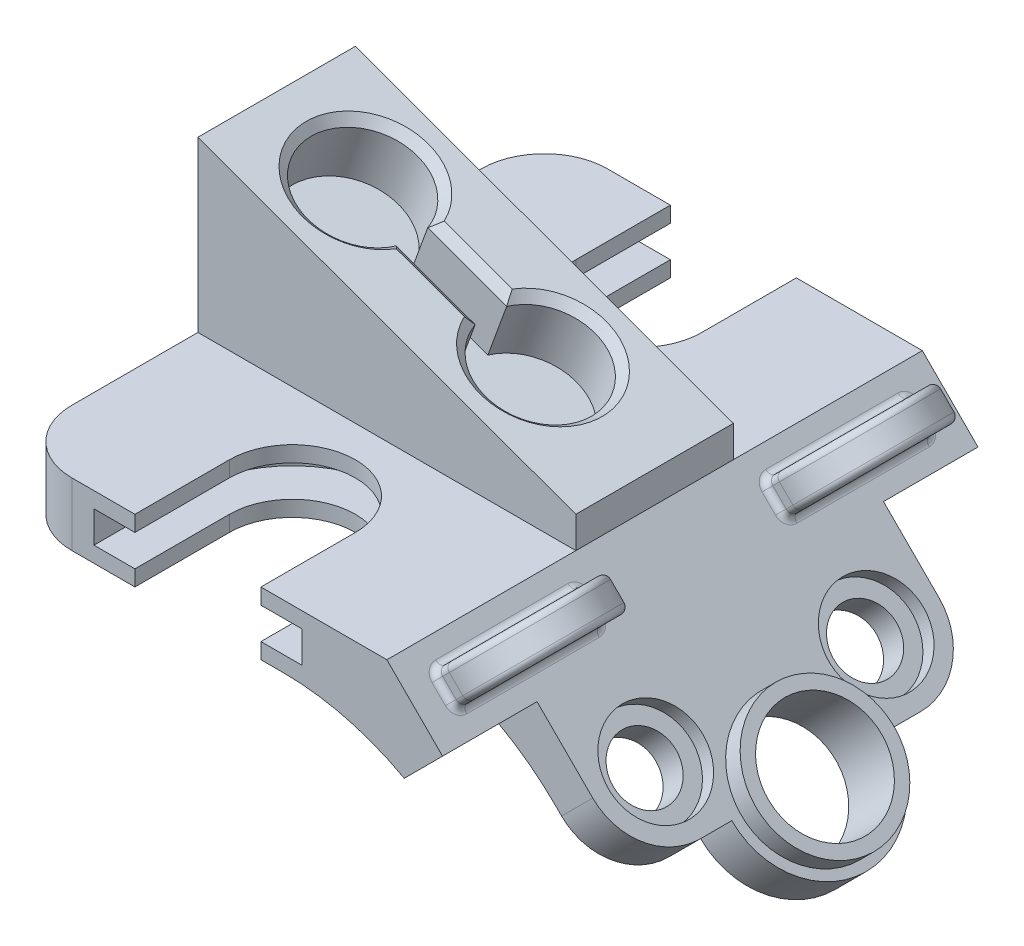
SolidWorks part; units mm, degrees
material "Alloy Steel (SS)"
ref_plane "Front Plane" through (0, 0, 0) normal (0, 0, 1) x (1, 0, 0)
ref_plane "Top Plane" through (0, 0, 0) normal (0, 1, 0) x (1, 0, 0)
ref_plane "Right Plane" through (0, 0, 0) normal (1, 0, 0) x (0, 0, -1)
sketch "Sketch1" plane through (0, 0, 0) normal (0, 0, 1) x (1, 0, 0)
  line L0 (0, 0) -> (0, 12.7)
  line L1 (0, 12.7) -> (76.2, 12.7)
  line L2 (76.2, 12.7) -> (118.8562, -29.9562)
  line L3 (118.8562, -29.9562) -> (112.57, -36.2424)
  line L4 (112.57, -36.2424) -> (91.2066, -14.879)
  line L5 (55.2856, 0) -> (0, 0)
  arc A0 (91.2066, -14.879) -> (55.2856, 0) centre (55.2856, -50.8) ccw
  dimension "D6" = 50.8
  dimension "D1" = 8.89
  dimension "D2" = 135
  dimension "D3" = 12.7
  dimension "D4" = 76.2
  dimension "D5" = 60.325
extrude "Boss-Extrude1" add sketch "Sketch1" along normal mid plane 107.95
sketch "Sketch2" plane through (0, 12.7, 0) normal (0, 1, 0) x (1, 0, 0)
  line L0 (25.4, 53.975) -> (25.4, 34.925)
  line L1 (76.2, 53.975) -> (0, 53.975) construction
  line L2 (50.8, 53.975) -> (50.8, 34.925)
  line L3 (25.4, 53.975) -> (50.8, 53.975)
  line L4 (0, -53.975) -> (0, 53.975) construction
  line L5 (0, 0) -> (76.2, 0) construction
  line L6 (76.2, -53.975) -> (76.2, 53.975) construction
  line L7 (25.4, -53.975) -> (50.8, -53.975)
  line L8 (50.8, -53.975) -> (50.8, -34.925)
  line L9 (25.4, -53.975) -> (25.4, -34.925)
  arc A0 (25.4, 34.925) -> (50.8, 34.925) centre (38.1, 34.925) ccw
  arc A1 (25.4, -34.925) -> (50.8, -34.925) centre (38.1, -34.925) cw
  point P8 (38.1, 53.975)
  dimension "D1" = 19.05
  dimension "D2" = 12.7
  dimension "D3" = 25.4
extrude "Cut-Extrude1" cut sketch "Sketch2" against normal through all
ref_plane "Plane1" through (0, 6.35, 0) normal (0, 1, 0) x (1, 0, 0)
sketch "Sketch4" plane through (0, 6.35, 0) normal (0, 1, 0) x (1, 0, 0)
  line L0 (59.055, -34.925) -> (59.055, -53.975)
  line L1 (76.2, -53.975) -> (50.8, -53.975) construction
  line L2 (59.055, -53.975) -> (17.145, -53.975)
  line L3 (17.145, -53.975) -> (17.145, -34.925)
  line L4 (25.4, -53.975) -> (0, -53.975) construction
  line L5 (0, 0) -> (76.2, 0) construction
  line L6 (50.8, -53.975) -> (50.8, -34.925) construction
  line L7 (76.2, -53.975) -> (76.2, 53.975) construction
  line L8 (25.4, -34.925) -> (25.4, -53.975) construction
  line L9 (17.145, 53.975) -> (17.145, 34.925)
  line L10 (59.055, 53.975) -> (17.145, 53.975)
  line L11 (59.055, 34.925) -> (59.055, 53.975)
  arc A0 (59.055, -34.925) -> (17.145, -34.925) centre (38.1, -34.925) ccw
  arc A1 (59.055, 34.925) -> (17.145, 34.925) centre (38.1, 34.925) cw
  dimension "D1" = 8.255
extrude "Cut-Extrude2" cut sketch "Sketch4" against normal mid plane 6.35
sketch "Sketch5" plane through (0, 0, 0) normal (0, 0, 1) x (1, 0, 0)
  line L0 (0, 12.7) -> (0, 46.7845)
  line L1 (0, 46.7845) -> (76.2, 19.05)
  line L2 (76.2, 19.05) -> (76.2, 12.7)
  line L3 (76.2, 12.7) -> (0, 12.7)
  dimension "D1" = 6.35
  dimension "D2" = 20
extrude "Boss-Extrude2" add sketch "Sketch5" along normal mid plane 31.75
sketch "Sketch6" plane through (15.0363, 41.3118, 0) normal (0.342, 0.9397, 0) x (0.9397, -0.342, 0)
  line L0 (-16.0013, -15.875) -> (-16.0013, 15.875) construction
  line L1 (13.6317, 3.175) -> (30.5658, 3.175)
  line L2 (13.6317, -3.175) -> (30.5658, -3.175)
  line L3 (3.0487, 0) -> (41.1487, 0) construction
  arc A0 (13.6317, 3.175) -> (13.6317, -3.175) centre (3.0487, 0) ccw
  arc A1 (30.5658, -3.175) -> (30.5658, 3.175) centre (41.1487, 0) ccw
  dimension "D1" = 22.098
  dimension "D2" = 19.05
  dimension "D3" = 38.1
  dimension "D4" = 6.35
  dimension "D5" = 3.175
extrude "Cut-Extrude3" cut sketch "Sketch6" against normal blind 12.7
chamfer "Chamfer1" distance 1.651 angle 45 4 edges at (64.0861, 23.4591, 0) (35.8023, 33.7536, 3.175) (7.5185, 44.048, 0) (35.8023, 33.7536, -3.175)
sketch "Sketch7" plane through (44.45, 44.45, 0) normal (0.7071, 0.7071, 0) x (0, 0, -1)
  line L0 (-53.975, -44.9013) -> (-53.975, -60.7763) construction
  line L1 (-53.975, -105.2263) -> (-53.975, -44.9013) construction
  line L2 (-53.975, -60.7763) -> (-34.925, -60.7763)
  line L3 (-34.925, -60.7763) -> (-34.925, -89.3513)
  line L4 (-34.925, -89.3513) -> (-15.875, -89.3513)
  line L8 (15.875, -89.3513) -> (34.925, -89.3513)
  line L9 (34.925, -89.3513) -> (34.925, -60.7763)
  line L10 (34.925, -60.7763) -> (53.975, -60.7763)
  line L11 (53.975, -105.2263) -> (53.975, -44.9013) construction
  line L12 (53.975, -60.7763) -> (53.975, -44.9013) construction
  line L13 (53.975, -44.9013) -> (-53.975, -44.9013) construction
  line L14 (-53.975, -60.7763) -> (-53.975, -105.2263)
  line L15 (-53.975, -105.2263) -> (53.975, -105.2263) construction
  line L17 (53.975, -105.2263) -> (53.975, -60.7763)
  arc A0 (-15.875, -89.3513) -> (15.875, -89.3513) centre (0, -89.3513) ccw
  line M16 (53.975, -105.2263) -> (53.975, -44.9013)
  line M20 (-53.975, -44.9013) -> (-53.975, -105.2263)
  line M21 (-53.975, -105.2263) -> (53.975, -105.2263)
  dimension "D5" = 15.875
  dimension "D1" = 15.875
  dimension "D2" = 19.05
  dimension "D3" = 28.575
  dimension "D4" = 19.05
  dimension "D6" = 53.975
extrude "Cut-Extrude4" cut sketch "Sketch7" against normal blind 12.7 contours A0 L4 L3 L2 M20 M21 | A0 L10 L9 L8 M21 M16
fillet "Fillet1" radius 12.7 4 edges at (0, 6.35, 53.975) (0, 6.35, -53.975) (104.4878, -21.874, -34.925) (104.4878, -21.874, 34.925)
sketch "Sketch9" plane through (44.45, 44.45, 0) normal (0.7071, 0.7071, 0) x (0, 0, -1)
  circle A0 centre (-22.225, -76.6513) radius 6.35
  circle A1 centre (22.225, -76.6513) radius 6.35
  dimension "D1" = 12.7
extrude "Cut-Extrude5" cut sketch "Sketch9" against normal blind 12.7
sketch "Sketch10" plane through (44.45, 44.45, 0) normal (0.7071, 0.7071, 0) x (0, 0, -1)
  circle A0 centre (-22.225, -76.6513) radius 9.525
  circle A1 centre (22.225, -76.6513) radius 9.525
  dimension "D1" = 19.05
extrude "Cut-Extrude6" cut sketch "Sketch10" against normal blind 3.175
sketch "Sketch11" plane through (44.45, 44.45, 0) normal (0.7071, 0.7071, 0) x (0, 0, -1)
  circle A0 centre (0, -89.3513) radius 13.97
  dimension "D1" = 27.94
extrude "Boss-Extrude3" add sketch "Sketch11" along normal mid plane 8.255
sketch "Sketch12" plane through (47.3686, 47.3686, 0) normal (0.7071, 0.7071, 0) x (0, 0, -1)
  circle A0 centre (0, -89.3513) radius 11.43
  dimension "D1" = 22.86
extrude "Cut-Extrude7" cut sketch "Sketch12" against normal through all
sketch "Sketch13" plane through (44.45, 44.45, 0) normal (0.7071, 0.7071, 0) x (0, 0, -1)
  line L0 (-53.975, -60.7763) -> (-53.975, -44.9013) construction
  line L1 (-47.879, -49.6638) -> (-18.669, -49.6638)
  line L2 (-47.879, -49.6638) -> (-47.879, -56.0138)
  line L3 (-47.879, -56.0138) -> (-18.669, -56.0138)
  line L4 (-18.669, -49.6638) -> (-18.669, -56.0138)
  line L5 (-47.879, -49.6638) -> (-18.669, -56.0138) construction
  line L6 (-47.879, -56.0138) -> (-18.669, -49.6638) construction
  line L8 (0, -44.9013) -> (0, -105.2263) construction
  line L9 (-15.875, -44.9013) -> (15.875, -44.9013) construction
  line L10 (47.879, -56.0138) -> (18.669, -49.6638) construction
  line L11 (47.879, -49.6638) -> (18.669, -56.0138) construction
  line L12 (18.669, -49.6638) -> (18.669, -56.0138)
  line L13 (47.879, -56.0138) -> (18.669, -56.0138)
  line L14 (47.879, -49.6638) -> (47.879, -56.0138)
  line L15 (47.879, -49.6638) -> (18.669, -49.6638)
  line L16 (-53.975, -44.9013) -> (-15.875, -44.9013) construction
  arc A0 (-15.875, -89.3513) -> (15.875, -89.3513) centre (0, -89.3513) ccw construction
  point P0 (-33.274, -52.8388)
  point P20 (33.274, -52.8388)
  dimension "D1" = 20.701
  dimension "D2" = 29.21
  dimension "D3" = 6.35
  dimension "D4" = 4.7625
extrude "Boss-Extrude4" add sketch "Sketch13" along normal blind 17.78
sketch "Sketch14" plane through (39.6077, -39.6077, 0) normal (0.7071, -0.7071, 0) x (0, 0, -1)
  line L0 (-44.704, 66.0368) -> (-21.844, 66.0368)
  line L2 (-47.879, 66.0368) -> (-47.879, 80.6418)
  line L3 (-47.879, 80.6418) -> (-18.669, 80.6418)
  line L4 (-18.669, 80.6418) -> (-18.669, 66.0368)
  line L5 (-22.225, 62.8618) -> (-34.925, 62.8618) construction
  line L6 (-44.704, 66.0368) -> (-47.879, 66.0368)
  line L7 (-21.844, 66.0368) -> (-18.669, 66.0368)
  line L8 (0, 45.6648) -> (0, -45.6648) construction
  line L9 (21.844, 66.0368) -> (18.669, 66.0368)
  line L10 (44.704, 66.0368) -> (47.879, 66.0368)
  line L11 (18.669, 80.6418) -> (18.669, 66.0368)
  line L12 (47.879, 80.6418) -> (18.669, 80.6418)
  line L13 (47.879, 66.0368) -> (47.879, 80.6418)
  line L14 (44.704, 66.0368) -> (21.844, 66.0368)
  arc A1 (-21.844, 66.0368) -> (-44.704, 66.0368) centre (-33.274, 66.0368) ccw
  arc A2 (-18.669, 66.0368) -> (-47.879, 66.0368) centre (-33.274, 66.0368) ccw
  arc A3 (18.669, 66.0368) -> (47.879, 66.0368) centre (33.274, 66.0368) cw
  arc A4 (21.844, 66.0368) -> (44.704, 66.0368) centre (33.274, 66.0368) cw
  point P12 (-33.274, 80.6418)
  line M4 (-18.669, 62.8618) -> (-18.669, 80.6418)
  line M5 (-18.669, 80.6418) -> (-47.879, 80.6418)
  line M6 (-47.879, 80.6418) -> (-47.879, 62.8618)
  dimension "D1" = 3.175
  dimension "D2" = 29.21
  dimension "D3" = 22.86
extrude "Cut-Extrude8" cut sketch "Sketch14" against normal through all contours A2 M4 M5 | A2 L3 M6 | L0 A1 | L11 A3 L12 | L12 A3 L13 | A4 L14
fillet "Fillet3" radius 1.905 4 edges at (84.0577, 9.3324, -21.844) (84.0577, 9.3324, -44.704) (84.0577, 9.3324, 21.844) (84.0577, 9.3324, 44.704)
fillet "Fillet4" radius 1.27 20 edges at (81.8127, 7.0873, 47.879) (85.1803, 5.9648, -18.669) (96.6301, 17.4146, -33.274) (80.6901, 10.4549, -18.669) (92.14, 21.9048, -33.274) (80.6901, 10.4549, 18.669) (85.1803, 5.9648, 18.669) (85.1803, 5.9648, 47.879) (81.8127, 7.0873, -18.669) (85.1803, 5.9648, -47.879) (84.0577, 4.8423, -33.274) (81.8127, 7.0873, -47.879) (79.5676, 9.3324, -33.274) (80.6901, 10.4549, -47.879) (80.6901, 10.4549, 47.879) (79.5676, 9.3324, 33.274) (92.14, 21.9048, 33.274) (96.6301, 17.4146, 33.274) (81.8127, 7.0873, 18.669) (84.0577, 4.8423, 33.274)
